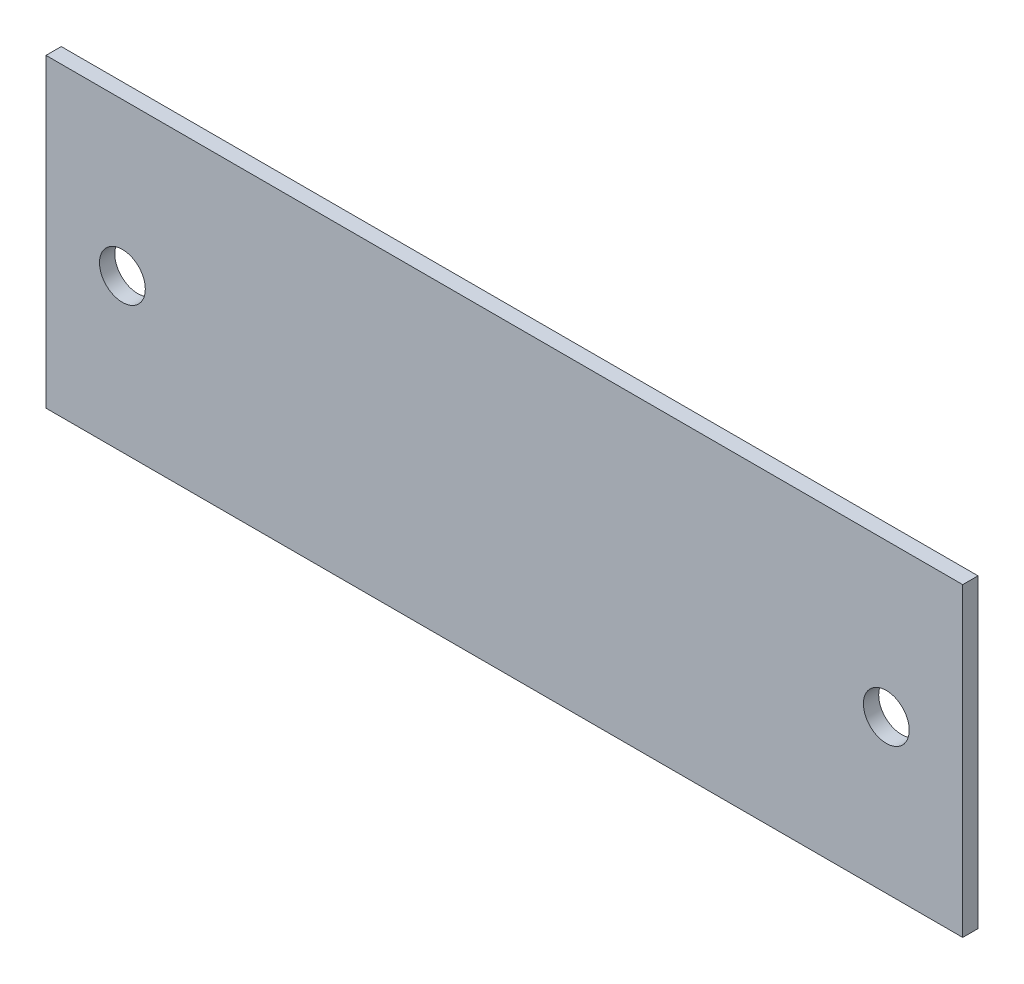
SolidWorks part; units mm, degrees
ref_plane "Plano frontal" through (0, 0, 0) normal (0, 0, 1) x (1, 0, 0)
ref_plane "Plano superior" through (0, 0, 0) normal (0, 1, 0) x (1, 0, 0)
ref_plane "Plano direito" through (0, 0, 0) normal (1, 0, 0) x (0, 0, -1)
sketch "Esboço1" plane through (0, 0, 0) normal (0, 0, 1) x (1, 0, 0)
  line L1 (-72.6247, -28.6398) -> (-12.6247, -28.6398)
  line L2 (-72.6247, -28.6398) -> (-72.6247, -8.6398)
  line L3 (-72.6247, -8.6398) -> (-12.6247, -8.6398)
  line L4 (-12.6247, -28.6398) -> (-12.6247, -8.6398)
extrude "Ressalto-extrusão1" add sketch "Esboço1" along normal blind 1
sketch "Esboço2" plane through (0, 0, 1) normal (0, 0, 1) x (1, 0, 0)
  line L0 (-42.6247, -28.6398) -> (-42.6247, -8.6398) construction
  line L1 (-72.6247, -28.6398) -> (-12.6247, -28.6398) construction
  line L2 (-12.6247, -8.6398) -> (-72.6247, -8.6398) construction
  line L3 (-72.6247, -8.6398) -> (-72.6247, -28.6398) construction
  circle A0 centre (-67.6247, -18.6398) radius 1.5
  circle A1 centre (-17.6247, -18.6398) radius 1.5
  dimension "D1" = 5
extrude "Corte-extrusão1" cut sketch "Esboço2" against normal through all
